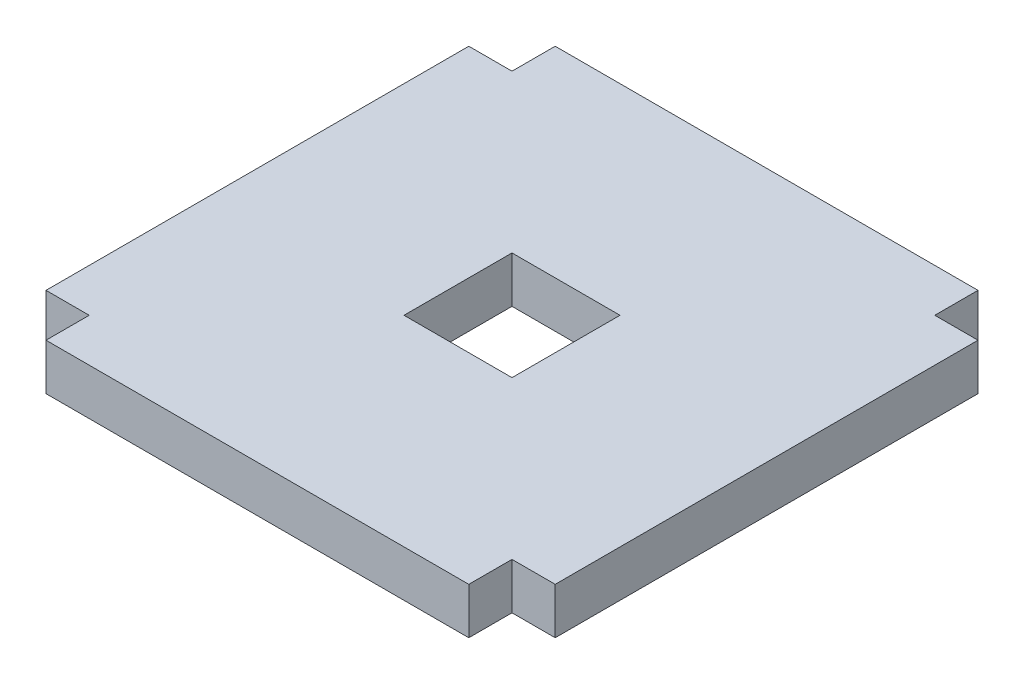
SolidWorks part; units mm, degrees
ref_plane "Front Plane" through (0, 0, 0) normal (0, 0, 1) x (1, 0, 0)
ref_plane "Top Plane" through (0, 0, 0) normal (0, 1, 0) x (1, 0, 0)
ref_plane "Right Plane" through (0, 0, 0) normal (1, 0, 0) x (0, 0, -1)
sketch "Sketch1" plane through (0, 0, 0) normal (0, 1, 0) x (1, 0, 0)
  line L0 (-104.775, 86.995) -> (-86.995, 86.995)
  line L1 (-104.775, -104.775) -> (104.775, -104.775)
  line L2 (-104.775, -104.775) -> (-104.775, 104.775)
  line L3 (-104.775, 104.775) -> (104.775, 104.775)
  line L4 (104.775, -104.775) -> (104.775, 104.775)
  line L5 (-104.775, -104.775) -> (104.775, 104.775) construction
  line L6 (-104.775, 104.775) -> (104.775, -104.775) construction
  line L7 (-86.995, 86.995) -> (-86.995, 104.775)
  line L8 (104.775, 86.995) -> (86.995, 86.995)
  line L9 (86.995, 86.995) -> (86.995, 104.775)
  line L10 (104.775, -86.995) -> (86.995, -86.995)
  line L11 (86.995, -86.995) -> (86.995, -104.775)
  line L12 (-86.995, -104.775) -> (-86.995, -86.995)
  line L13 (-86.995, -86.995) -> (-104.775, -86.995)
  line L15 (-22.225, -22.225) -> (22.225, -22.225)
  line L16 (-22.225, -22.225) -> (-22.225, 22.225)
  line L17 (-22.225, 22.225) -> (22.225, 22.225)
  line L18 (22.225, -22.225) -> (22.225, 22.225)
  line L19 (-22.225, -22.225) -> (22.225, 22.225) construction
  line L20 (-22.225, 22.225) -> (22.225, -22.225) construction
  point P0 (0, 0)
  point P17 (0, 0)
  dimension "D1" = 209.55
  dimension "D2" = 17.78
  dimension "D3" = 44.45
extrude "Boss-Extrude1" add sketch "Sketch1" along normal blind 19.05 contours L13 L12 L1 L11 L10 L4 L8 L9 L3 L7 L0 L2
